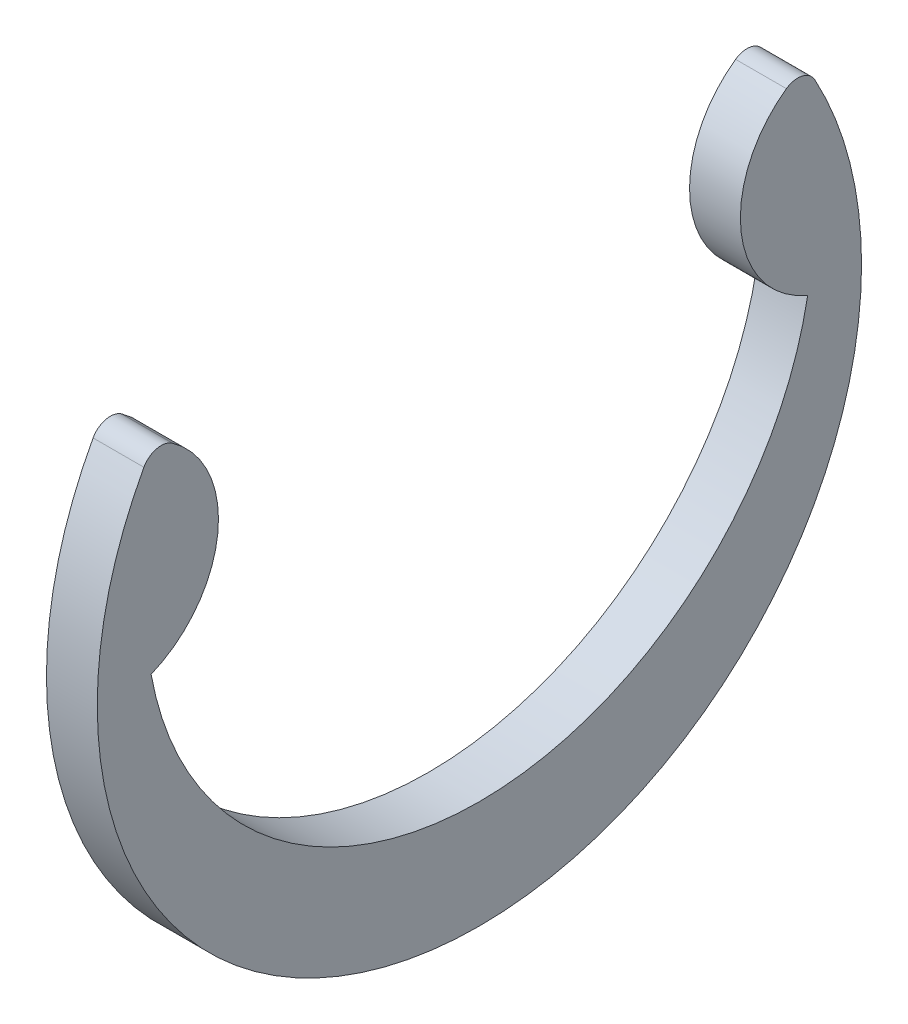
SolidWorks part; units mm, degrees
material "Cast Carbon Steel"
ref_plane "Front" through (0, 0, 0) normal (0, 0, 1) x (1, 0, 0)
ref_plane "Top" through (0, 0, 0) normal (0, 1, 0) x (1, 0, 0)
ref_plane "Right" through (0, 0, 0) normal (1, 0, 0) x (0, 0, -1)
sketch "Sketch1" plane through (0, 0, 0) normal (1, 0, 0) x (0, 0, -1)
  circle A0 centre (0, 0) radius 3.429 construction
  arc A1 (-4.1021, 0) -> (4.1021, 0) centre (0, 0.7392) ccw
  circle A2 centre (0, 0) radius 4.7752 construction
  circle A3 centre (0, 0) radius 4.953 construction
  arc A4 (4.1925, 2.286) -> (-4.1925, 2.286) centre (0, 0) cw
  arc A5 (-3.8364, 2.3687) -> (-4.1021, 0) centre (-4.6215, 1.2575) cw
  arc A6 (-4.1925, 2.286) -> (-3.8364, 2.3687) centre (-3.9776, 2.1689) cw
  arc A7 (4.1925, 2.286) -> (3.8364, 2.3687) centre (3.9776, 2.1689) ccw
  arc A8 (4.1021, 0) -> (3.8364, 2.3687) centre (4.6215, 1.2575) cw
  arc A9 (3.8364, 2.3687) -> (4.1021, 0) centre (0, 0.7392) cw construction
  dimension "A" = 6.858
  dimension "OD" = 9.5504
  dimension "D1" = 2.286
  dimension "D2" = 8.2042
extrude "Extrude1" add sketch "Sketch1" along normal mid plane 0.635
sketch "Sketch2" plane through (0, 0, 0) normal (0, 0, 1) x (1, 0, 0)
  line L0 (-1.8415, 0) -> (5.5245, 0)
  line L1 (5.5245, 0) -> (5.5245, -3.9624)
  line L3 (5.5245, -3.9624) -> (0.3683, -3.9624)
  line L4 (0.3683, -3.9624) -> (0.3683, -3.5052)
  line L5 (0.3683, -3.5052) -> (-0.3683, -3.5052)
  line L6 (-0.3683, -3.5052) -> (-0.3683, -3.9624)
  line L7 (-0.3683, -3.9624) -> (-1.8415, -3.9624) construction
  line L8 (-1.8415, -3.9624) -> (-1.8415, 0) construction
  line L9 (0, -3.5052) -> (0, 0) construction
  line L10 (5.5245, 0) -> (14.0551, 0) construction
  line L11 (-0.3683, -3.9624) -> (-1.6129, -3.9624)
  line L12 (-1.6129, -3.9624) -> (-1.8415, -3.7338)
  line L13 (-1.8415, -3.7338) -> (-1.8415, 0)
  point P14 (-0.3683, -3.7338)
  dimension "D2" = 7.366
  dimension "D3" = 1.8415
  dimension "D4" = 45
revolve "Revolve1" [suppressed] add sketch "Sketch2" angle 360 about L10
equation "\"D2@Sketch2\" = \"W@Sketch2\"*10"
equation "\"D3@Sketch2\" = \"D2@Sketch2\"/4"
equation "\"D1@Sketch1\" = \"A@Sketch1\"/3"
equation "\"D2@Sketch1\" = (\"OD@Sketch1\"+\"A@Sketch1\")/2"
